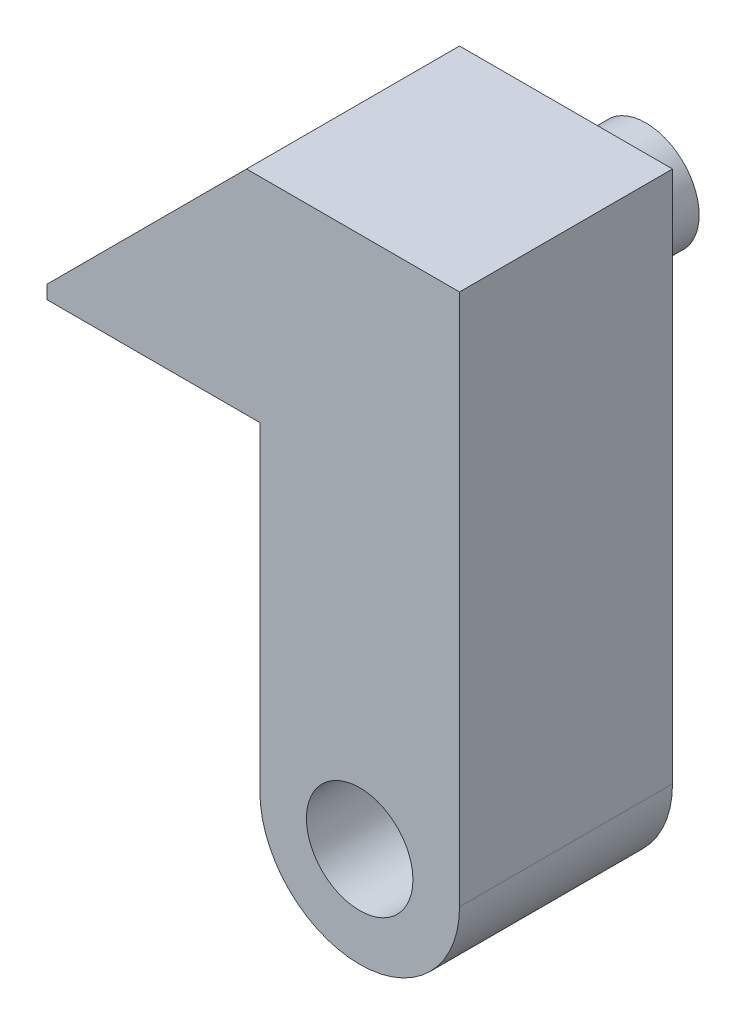
SolidWorks part; units mm, degrees
ref_plane "Front Plane" through (0, 0, 0) normal (0, 0, 1) x (1, 0, 0)
ref_plane "Top Plane" through (0, 0, 0) normal (0, 1, 0) x (1, 0, 0)
ref_plane "Right Plane" through (0, 0, 0) normal (1, 0, 0) x (0, 0, -1)
sketch "Sketch1" plane through (0, 0, 0) normal (0, 0, 1) x (1, 0, 0)
  line L0 (0, 0) -> (0, 19.05)
  line L1 (0, 19.05) -> (-12.7, 19.05)
  line L2 (-12.7, 19.05) -> (-12.7, 19.8437)
  line L3 (-12.7, 19.8437) -> (-0.7937, 31.75)
  line L4 (-0.7937, 31.75) -> (11.9062, 31.75)
  line L5 (11.9062, 31.75) -> (11.9062, 0)
  arc A0 (0, 0) -> (11.9062, 0) centre (5.9531, 0) ccw
  circle A1 centre (5.9531, 0) radius 3.175
  dimension "D1" = 11.9062
  dimension "D7" = 6.35
  dimension "D2" = 31.75
  dimension "D3" = 12.7
  dimension "D4" = 0.7937
  dimension "D5" = 45
  dimension "D6" = 12.7
extrude "Boss-Extrude1" add sketch "Sketch1" along normal blind 12.7
sketch "Sketch2" plane through (0, 0, 0) normal (0, 0, -1) x (-1, 0, 0)
  line L0 (-11.9062, 0) -> (-11.9062, 31.75) construction
  line L1 (-11.9062, 31.75) -> (0.7937, 31.75) construction
  circle A0 centre (-5.5562, 25.4) radius 3.175
  dimension "D1" = 6.35
  dimension "D2" = 6.35
  dimension "D3" = 6.35
extrude "Boss-Extrude2" add sketch "Sketch2" along normal blind 4.7625
ref_plane "Plane1" through (-12.1669, 12.1669, 0) normal (-0.7071, 0.7071, 0) x (0, 0, 1)
sketch "Sketch3" plane through (-12.1669, 12.1669, 0) normal (-0.7071, 0.7071, 0) x (0, 0, 1)
  line L0 (0, 25.0644) -> (-4.7625, 25.0644) construction
  line L1 (-3.175, 25.0644) -> (-1.5875, 25.0644)
  line L2 (-3.175, 25.0644) -> (-3.175, 24.2706)
  line L3 (-3.175, 24.2706) -> (-1.5875, 24.2706)
  line L4 (-1.5875, 25.0644) -> (-1.5875, 24.2706)
  line L5 (-4.7625, 25.0644) -> (-4.7625, 18.7144) construction
  dimension "D1" = 1.5875
  dimension "D2" = 1.5875
  dimension "D3" = 0.7937
extrude "Cut-Extrude1" cut sketch "Sketch3" against normal blind 9.525
